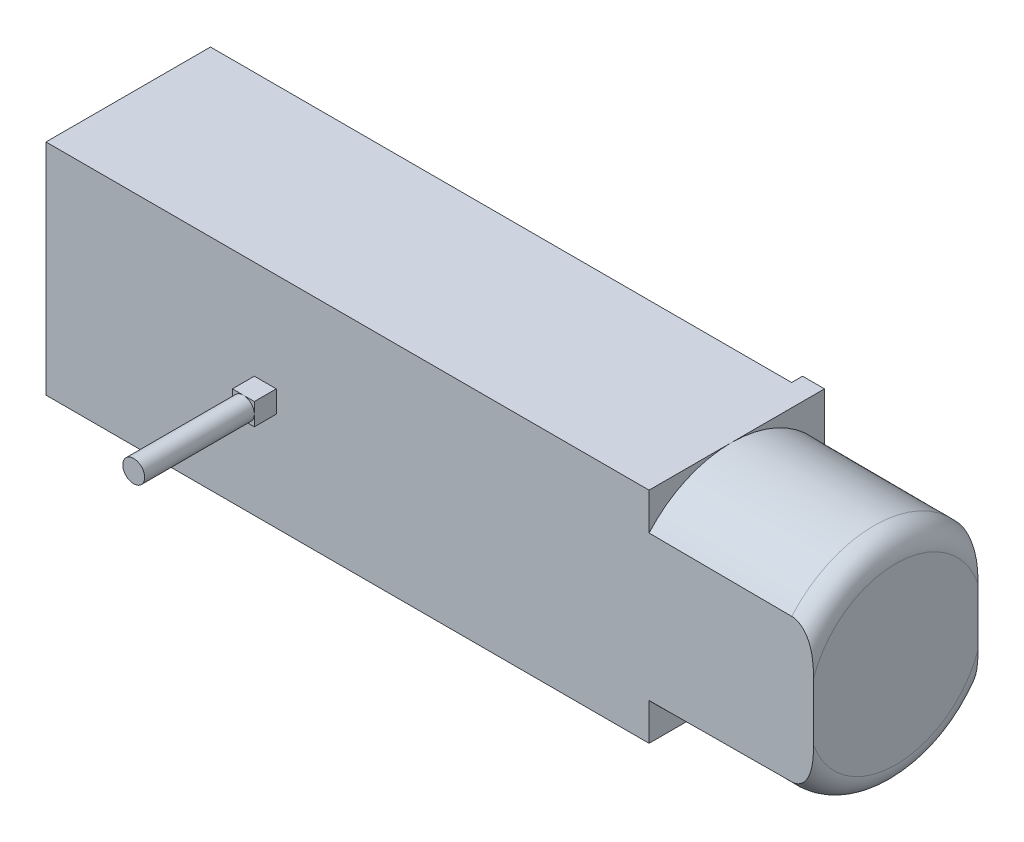
SolidWorks part; units mm, degrees
ref_plane "前视基准面" through (0, 0, 0) normal (0, 0, 1) x (1, 0, 0)
ref_plane "上视基准面" through (0, 0, 0) normal (0, 1, 0) x (1, 0, 0)
ref_plane "右视基准面" through (0, 0, 0) normal (1, 0, 0) x (0, 0, -1)
sketch "草图1" plane through (0, 0, 0) normal (1, 0, 0) x (0, 0, -1)
  line L1 (-7.5, -10) -> (7.5, -10)
  line L2 (-7.5, -10) -> (-7.5, 10)
  line L3 (-7.5, 10) -> (7.5, 10)
  line L4 (7.5, -10) -> (7.5, 10)
  line L5 (-7.5, -10) -> (7.5, 10) construction
  line L6 (-7.5, 10) -> (7.5, -10) construction
  point P0 (0, 0)
  dimension "D1" = 15
  dimension "D2" = 20
extrude "凸台-拉伸1" add sketch "草图1" along normal blind 55
sketch "草图2" plane through (0, 0, 0) normal (0, 0, 1) x (1, 0, 0)
  line L0 (55, 0) -> (70, 0)
  line L1 (55, 10) -> (55, -10) construction
  line L2 (16.5, 0) -> (-16.5, 0) construction
  line L3 (70, 0) -> (70, 7.9476)
  line L4 (68.0081, 9.9476) -> (55, 10)
  line L5 (55, 10) -> (55, 0)
  arc A0 (70, 7.9476) -> (68.0081, 9.9476) centre (68, 7.9476) ccw
  dimension "D1" = 2
  dimension "D2" = 15
revolve "旋转1" add sketch "草图2" angle 360 about L0
sketch "草图3" plane through (0, 0, -7.5) normal (0, 0, -1) x (-1, 0, 0)
  line L0 (-55, 10) -> (0, 10) construction
  line L1 (-55, 10) -> (-53, 10)
  line L2 (-55, 10) -> (-55, 4)
  line L3 (-55, 4) -> (-53, 4)
  line L4 (-53, 10) -> (-53, 4)
  line L5 (-55, -10) -> (-53, -10)
  line L6 (-55, -10) -> (-55, -4)
  line L7 (-55, -4) -> (-53, -4)
  line L8 (-53, -10) -> (-53, -4)
  line L9 (-55, -10) -> (0, -10) construction
  dimension "D1" = 2
  dimension "D2" = 2
  dimension "D3" = 6
  dimension "D4" = 6
extrude "凸台-拉伸2" add sketch "草图3" along normal blind 1
sketch "草图4" plane through (0, 0, 7.5) normal (0, 0, 1) x (1, 0, 0)
  line L0 (16.5, 0) -> (-16.5, 0) construction
  line L5 (19, -1) -> (21, -1)
  line L6 (19, -1) -> (19, 1)
  line L7 (19, 1) -> (21, 1)
  line L8 (21, -1) -> (21, 1)
  line L9 (19, -1) -> (21, 1) construction
  line L10 (19, 1) -> (21, -1) construction
  line L11 (0, -11) -> (0, 11) construction
  point P0 (20, 0)
  dimension "D1" = 20
  dimension "D2" = 2
  dimension "D3" = 2
extrude "凸台-拉伸3" add sketch "草图4" along normal blind 2
sketch "草图5" plane through (55, 0, 0) normal (-1, 0, 0) x (0, 0, 1)
  line L1 (-7.5, 10) -> (-14.1334, 10)
  line L2 (-7.5, 10) -> (-7.5, -10.2724)
  line L3 (-7.5, -10.2724) -> (-14.1334, -10.2724)
  line L4 (-14.1334, 10) -> (-14.1334, -10.2724)
  line L5 (7.5, 10) -> (19.6671, 10)
  line L6 (7.5, 10) -> (7.5, -13.0524)
  line L7 (7.5, -13.0524) -> (19.6671, -13.0524)
  line L8 (19.6671, 10) -> (19.6671, -13.0524)
extrude "切除-拉伸1" cut sketch "草图5" against normal blind 24
sketch "草图6" plane through (0, 0, 9.5) normal (0, 0, 1) x (1, 0, 0)
  line L0 (9.9, 0) -> (-9.9, 0) construction
  circle A0 centre (20, 0) radius 1
extrude "凸台-拉伸4" add sketch "草图6" along normal blind 10
